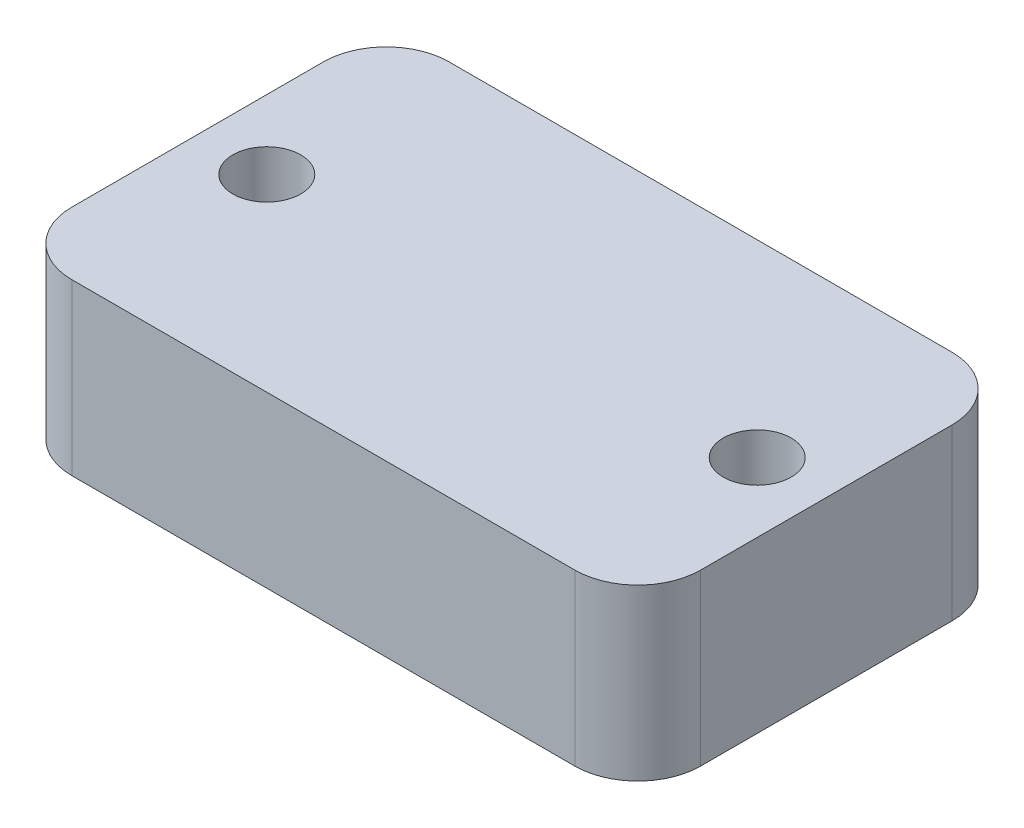
SolidWorks part; units mm, degrees
ref_plane "Front Plane" through (0, 0, 0) normal (0, 0, 1) x (1, 0, 0)
ref_plane "Top Plane" through (0, 0, 0) normal (0, 1, 0) x (1, 0, 0)
ref_plane "Right Plane" through (0, 0, 0) normal (1, 0, 0) x (0, 0, -1)
sketch "Sketch1" plane through (0, 0, 0) normal (0, 1, 0) x (1, 0, 0)
  line L0 (0, -55) -> (0, 55) construction
  line L1 (20, -15) -> (-20, -15)
  line L2 (25, -10) -> (25, 10)
  line L3 (20, 15) -> (-20, 15)
  line L4 (-25, -10) -> (-25, 10)
  line L5 (25, -15) -> (-25, 15) construction
  line L6 (25, 15) -> (-25, -15) construction
  circle A0 centre (-19.5, 0) radius 2.7
  circle A1 centre (19.5, 0) radius 2.7
  arc A2 (20, -15) -> (25, -10) centre (20, -10) ccw
  arc A3 (25, 10) -> (20, 15) centre (20, 10) ccw
  arc A4 (-20, -15) -> (-25, -10) centre (-20, -10) cw
  arc A5 (-20, 15) -> (-25, 10) centre (-20, 10) ccw
  point P0 (0, 0)
  dimension "D3" = 19.5
  dimension "D4" = 5
  dimension "D1" = 50
  dimension "D2" = 30
extrude "Boss-Extrude1" add sketch "Sketch1" along normal blind 13.5
